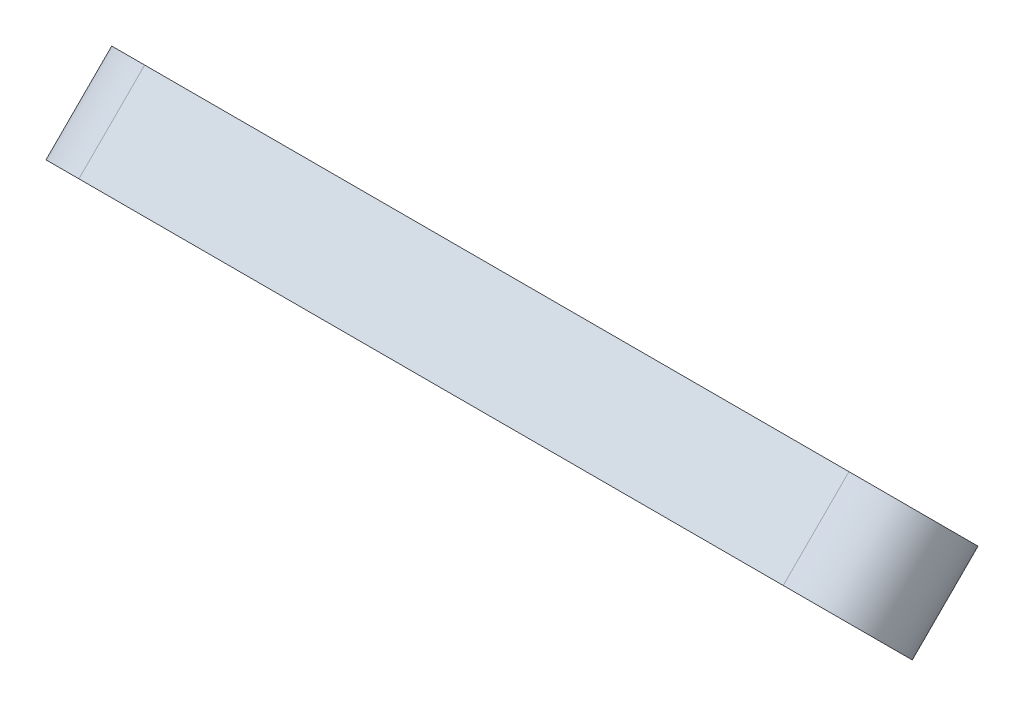
SolidWorks part; units mm, degrees
ref_plane "Front Plane" through (0, 0, 0) normal (0, 0, 1) x (1, 0, 0)
ref_plane "Top Plane" through (0, 0, 0) normal (0, 1, 0) x (1, 0, 0)
ref_plane "Right Plane" through (0, 0, 0) normal (1, 0, 0) x (0, 0, -1)
sketch "Sketch1" plane through (0, 37.9225, -37.9225) normal (0, 0.7071, -0.7071) x (-1, 0, 0)
  line L0 (-134.3836, 510.1317) -> (-36.7968, 508.2313) construction
  line L1 (-134.2076, 519.1686) -> (-36.6208, 517.2682)
  line L2 (-134.5596, 501.0948) -> (-36.9728, 499.1945)
  line L3 (-85.5902, 509.1815) -> (-85.5902, 448.7705) construction
  arc A0 (-134.2076, 519.1686) -> (-134.5596, 501.0948) centre (-134.3836, 510.1317) ccw
  arc A1 (-36.9728, 499.1945) -> (-36.6208, 517.2682) centre (-36.7968, 508.2313) ccw
  circle A2 centre (-134.3836, 510.1317) radius 2.3114
  circle A3 centre (-36.7968, 508.2313) radius 2.3114
  circle A4 centre (-60.1902, 508.6869) radius 2.286
  circle A5 centre (-110.9902, 509.6762) radius 2.286
  point P4 (-85.5902, 509.1815)
  dimension "D1" = 4.6228
  dimension "D2" = 4.6228
  dimension "D3" = 25.4
  dimension "D4" = 25.4
extrude "Boss-Extrude1" add sketch "Sketch1" along normal blind 12.7
